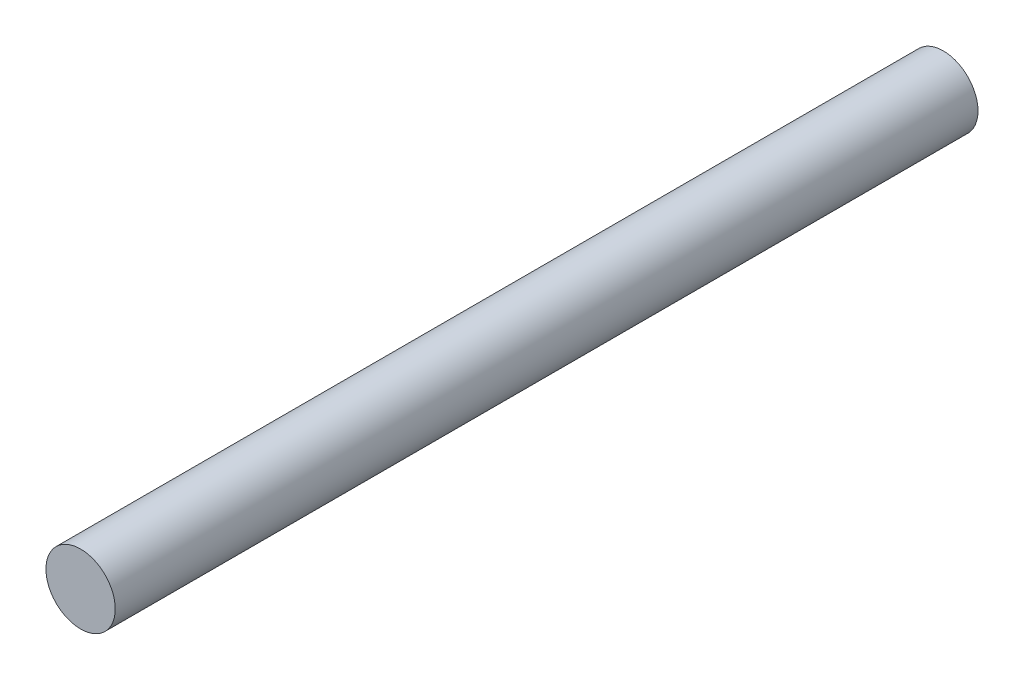
SolidWorks part; units mm, degrees
material "AISI Type 316L stainless steel"
ref_plane "Front Plane" through (0, 0, 0) normal (0, 0, 1) x (1, 0, 0)
ref_plane "Top Plane" through (0, 0, 0) normal (0, 1, 0) x (1, 0, 0)
ref_plane "Right Plane" through (0, 0, 0) normal (1, 0, 0) x (0, 0, -1)
sketch "Sketch1" plane through (0, 0, 0) normal (0, 0, 1) x (1, 0, 0)
  circle A0 centre (0, 0) radius 4
  dimension "D1" = 8
extrude "Boss-Extrude1" add sketch "Sketch1" along normal blind 99.568
